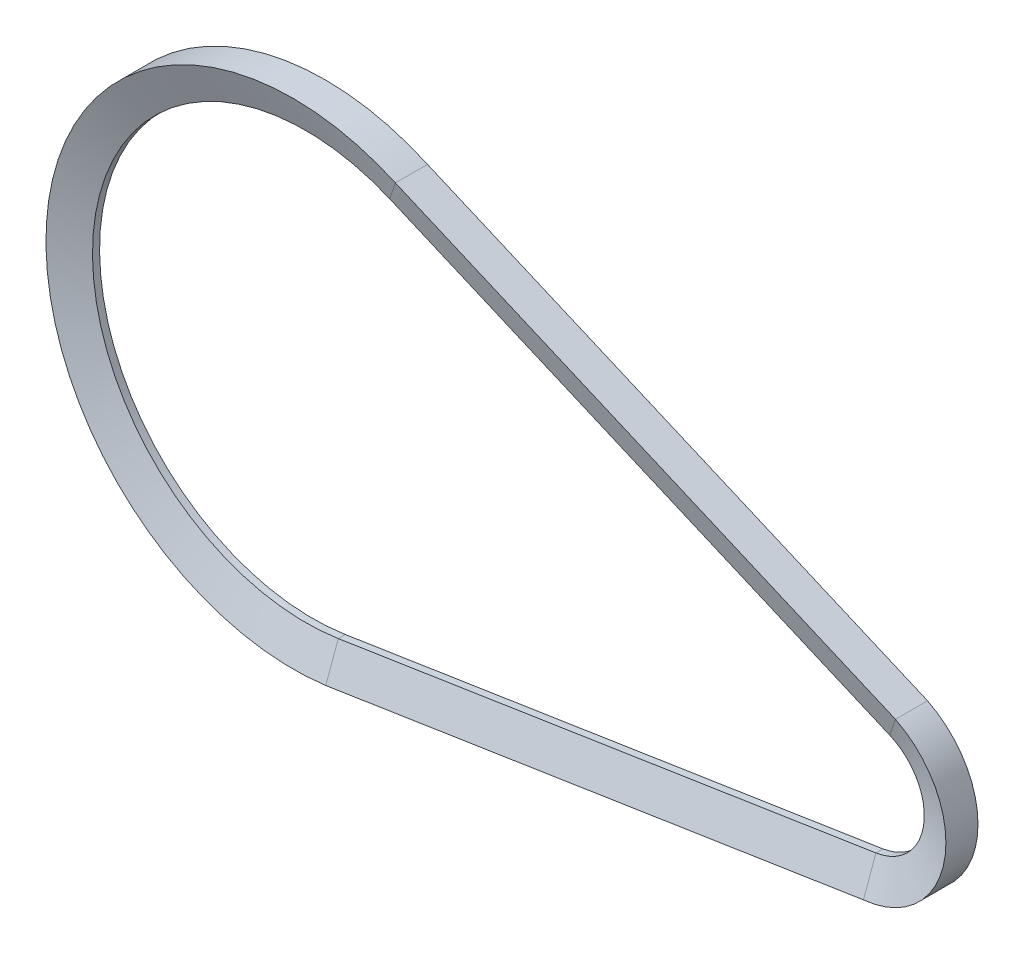
SolidWorks part; units mm, degrees
ref_plane "Front Plane" through (0, 0, 0) normal (0, 0, 1) x (1, 0, 0)
ref_plane "Top Plane" through (0, 0, 0) normal (0, 1, 0) x (1, 0, 0)
ref_plane "Right Plane" through (0, 0, 0) normal (1, 0, 0) x (0, 0, -1)
sketch "Sketch1" plane through (0, 0, 0) normal (0, 0, 1) x (1, 0, 0)
  line L0 (18.3322, 42.7338) -> (127.4083, -4.0584)
  line L1 (7.1106, -45.9531) -> (124.4038, -27.8036)
  arc A0 (18.3322, 42.7338) -> (7.1106, -45.9531) centre (0, 0) ccw
  arc A1 (124.4038, -27.8036) -> (127.4083, -4.0584) centre (122.5, -15.5) ccw
  dimension "D2" = 93
  dimension "D3" = 24.9
  dimension "D1" = 122.5
  dimension "D4" = 15.5
ref_plane "Plane1" through (7.1106, 0, 0) normal (1, 0, 0) x (0, 0, -1)
sketch "Sketch2" plane through (7.1106, 0, 0) normal (1, 0, 0) x (0, 0, -1)
  line L0 (0, -45.9531) -> (0, -16.1419) construction
  line L1 (-0.7702, -45.9531) -> (0.7702, -45.9531)
  line L2 (-3.5, -53.4531) -> (3.5, -53.4531)
  line L3 (3.5, -53.4531) -> (0.7702, -45.9531)
  line L4 (-0.7702, -45.9531) -> (-3.5, -53.4531)
  line L5 (0, -45.9531) -> (0, -53.4531) construction
  point P8 (0, 0)
  dimension "D1" = 7
  dimension "D2" = 7.5
  dimension "D3" = 40
sweep "Sweep1" add profiles "Sketch2" path "Sketch1"
